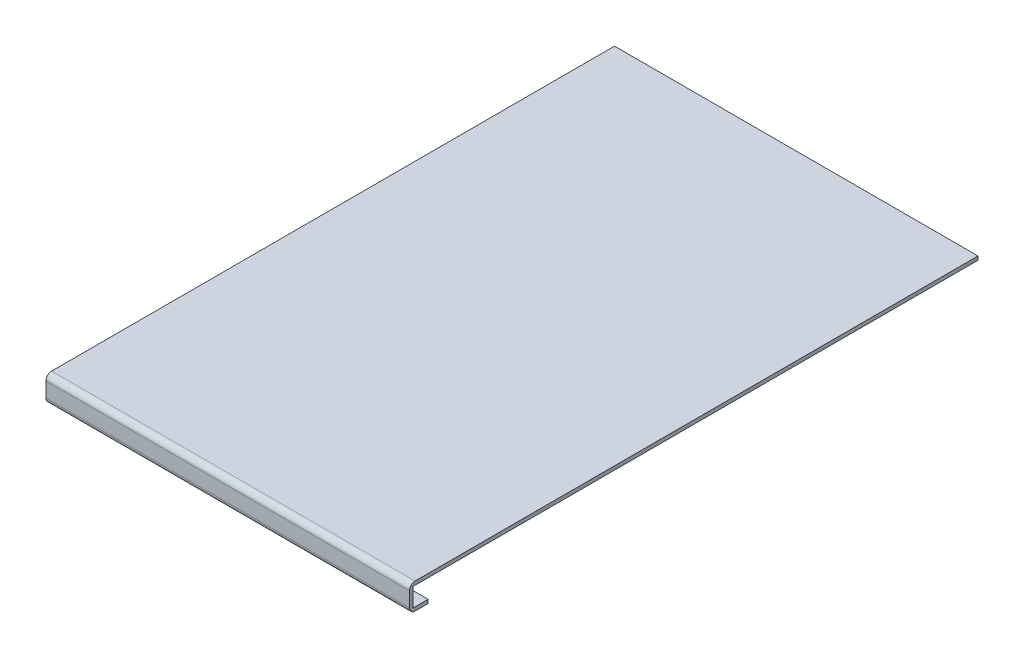
SolidWorks part; units mm, degrees
ref_plane "Plano frontal" through (0, 0, 0) normal (0, 0, 1) x (1, 0, 0)
ref_plane "Plano superior" through (0, 0, 0) normal (0, 1, 0) x (1, 0, 0)
ref_plane "Plano direito" through (0, 0, 0) normal (1, 0, 0) x (0, 0, -1)
sketch "Esboço1" plane through (0, 0, 0) normal (1, 0, 0) x (0, 0, -1)
  line L0 (0, 33.0938) -> (0, -54.4446) construction
  line L5 (0, 0) -> (-150, 0)
  line L6 (-150, 0) -> (-150, -14)
  line L7 (-150, -14) -> (-140, -14)
  line L8 (-148, -12) -> (-140, -12)
  line L9 (-140, -12) -> (-140, -14)
  line L10 (0, 0) -> (155, 0)
  line L11 (155, 0) -> (155, -2)
  line L12 (-148, -12) -> (-148, -2)
  line L13 (-148, -2) -> (0, -2)
  line L14 (155, -2) -> (0, -2)
  point P0 (0, 0)
  dimension "D1" = 2
  dimension "D2" = 2
  dimension "D3" = 10
  dimension "D4" = 8
  dimension "D5" = 155
  dimension "D6" = 150
extrude "Ressalto-extrusão1" add sketch "Esboço1" along normal blind 195
sketch "Esboço2" plane through (0, 0, -155) normal (0, 0, -1) x (-1, 0, 0)
  line L0 (-97.5, 4.1194) -> (-97.5, -20.4689) construction
  line L7 (-37.5, 0) -> (-157.5, 0)
  line L9 (-195, 0) -> (0, 0) construction
  line L10 (-157.5, 0) -> (-147.5, -12)
  line L11 (-195, -12) -> (0, -12) construction
  line L12 (-147.5, -12) -> (-47.5, -12)
  line L13 (-37.5, 0) -> (-47.5, -12)
  point P11 (-97.5, -12)
  point P12 (-97.5, 0)
  dimension "D1" = 60
  dimension "D2" = 50
extrude "Ressalto-extrusão2" add sketch "Esboço2" against normal blind 2 separate body
fillet "Filete1" radius 3 2 edges at (97.5, -14, 150) (97.5, 0, 150)
